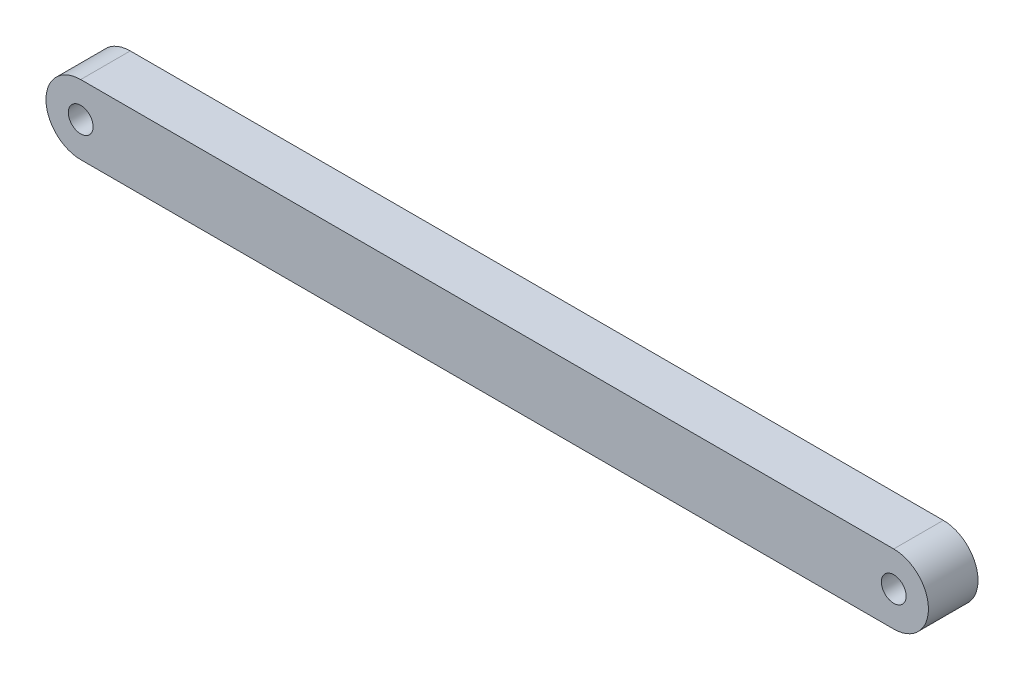
SolidWorks part; units mm, degrees
ref_plane "Front Plane" through (0, 0, 0) normal (0, 0, 1) x (1, 0, 0)
ref_plane "Top Plane" through (0, 0, 0) normal (0, 1, 0) x (1, 0, 0)
ref_plane "Right Plane" through (0, 0, 0) normal (1, 0, 0) x (0, 0, -1)
sketch "Sketch1" plane through (0, 0, 0) normal (0, 0, 1) x (1, 0, 0)
  line L0 (0, 0) -> (164, 0) construction
  line L1 (0, 7) -> (164, 7)
  line L2 (0, -7) -> (164, -7)
  arc A0 (0, 7) -> (0, -7) centre (0, 0) ccw
  arc A1 (164, -7) -> (164, 7) centre (164, 0) ccw
  circle A2 centre (0, 0) radius 2.5
  circle A3 centre (164, 0) radius 2.5
  point P3 (82, 0)
  dimension "D1" = 5
  dimension "D3" = 7
  dimension "D2" = 164
extrude "Boss-Extrude1" add sketch "Sketch1" along normal mid plane 10
